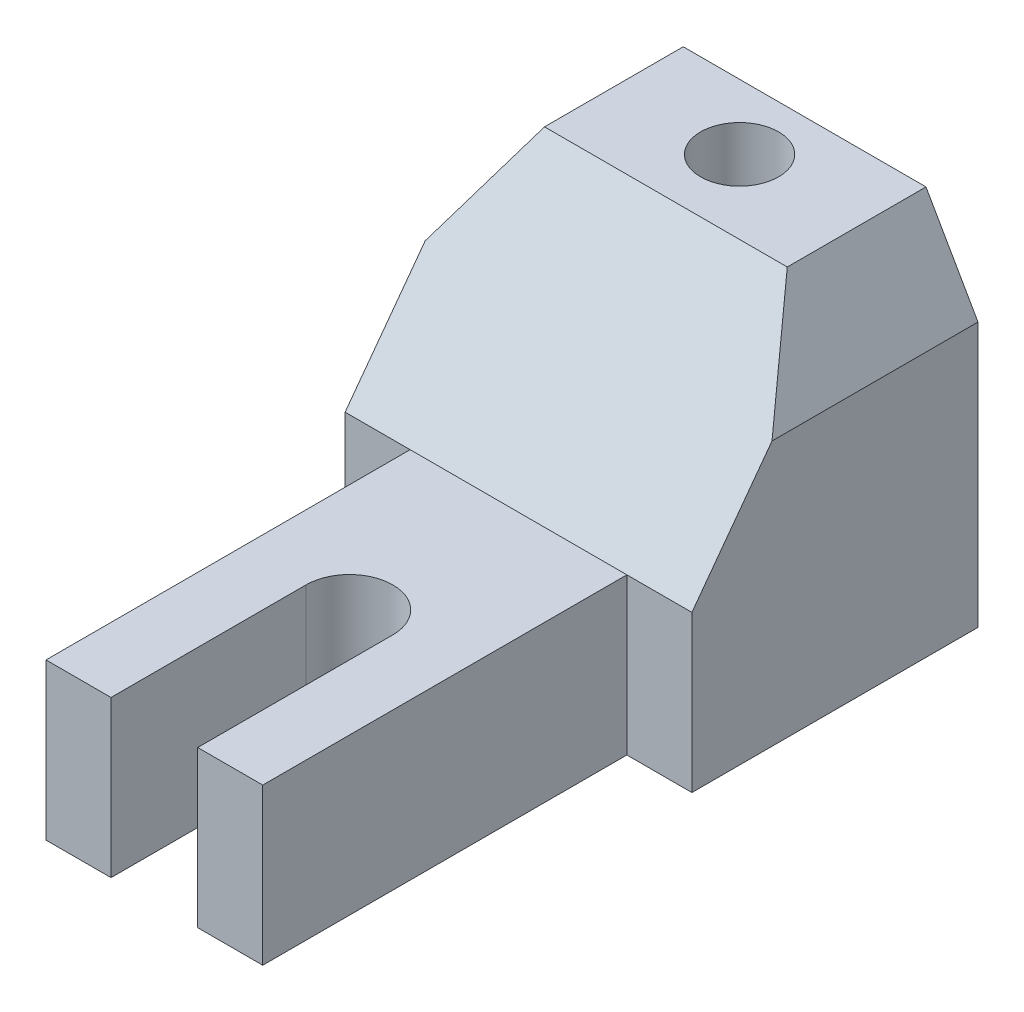
SolidWorks part; units mm, degrees
ref_plane "Alzado" through (0, 0, 0) normal (0, 0, 1) x (1, 0, 0)
ref_plane "Planta" through (0, 0, 0) normal (0, 1, 0) x (1, 0, 0)
ref_plane "Vista lateral" through (0, 0, 0) normal (1, 0, 0) x (0, 0, -1)
sketch "Croquis1" plane through (0, 0, 0) normal (0, 1, 0) x (1, 0, 0)
  line L1 (18.7624, -27.6609) -> (98.7624, -27.6609)
  line L2 (18.7624, -27.6609) -> (18.7624, 122.3391)
  line L3 (18.7624, 122.3391) -> (98.7624, 122.3391)
  line L4 (98.7624, -27.6609) -> (98.7624, 122.3391)
  dimension "D1" = 80
  dimension "D2" = 150
extrude "Saliente-Extruir1" add sketch "Croquis1" along normal blind 82
sketch "Croquis2" plane through (0, 0, -122.3391) normal (0, 0, -1) x (-1, 0, 0)
  line L0 (-98.7624, 82) -> (-98.7624, 61)
  line L1 (-98.7624, 82) -> (-98.7624, 0) construction
  line L2 (-98.7624, 61) -> (-86.7624, 82)
  line L3 (-98.7624, 82) -> (-18.7624, 82) construction
  line L4 (-86.7624, 82) -> (-98.7624, 82)
  line L5 (-18.7624, 82) -> (-30.7624, 82)
  line L6 (-30.7624, 82) -> (-18.7624, 61)
  line L7 (-18.7624, 82) -> (-18.7624, 0) construction
  line L8 (-18.7624, 61) -> (-18.7624, 82)
  dimension "D1" = 21
  dimension "D2" = 12
  dimension "D3" = 21
  dimension "D4" = 12
extrude "Cortar-Extruir1" cut sketch "Croquis2" against normal blind 150
sketch "Croquis3" plane through (0, 82, 0) normal (0, 1, 0) x (1, 0, 0)
  line L0 (98.7624, -27.6609) -> (98.7624, 122.3391) construction
  line L1 (86.7624, 122.3391) -> (30.7624, 122.3391) construction
  line L2 (30.7624, -27.6609) -> (86.7624, -27.6609) construction
  line L3 (48.7624, 17.3391) -> (48.7624, -27.6609)
  line L4 (68.7624, 17.3391) -> (68.7624, -27.6609)
  line L5 (18.7624, -27.6609) -> (18.7624, 122.3391) construction
  line L6 (18.7624, 56.3391) -> (33.7624, 56.3391)
  line L7 (18.7624, 56.3391) -> (18.7624, -27.6609)
  line L8 (18.7624, -27.6609) -> (33.7624, -27.6609)
  line L9 (33.7624, 56.3391) -> (33.7624, -27.6609)
  line L11 (98.7624, 56.3391) -> (83.7624, 56.3391)
  line L12 (98.7624, 56.3391) -> (98.7624, -27.6609)
  line L13 (98.7624, -27.6609) -> (83.7624, -27.6609)
  line L14 (83.7624, 56.3391) -> (83.7624, -27.6609)
  circle A0 centre (58.7624, 107.3391) radius 9
  arc A1 (68.7624, 17.3391) -> (48.7624, 17.3391) centre (58.7624, 17.3391) ccw
  line M1 (30.7624, -27.6609) -> (86.7624, -27.6609)
  line M2 (86.7624, -27.6609) -> (86.7624, 122.3391)
  line M4 (30.7624, 122.3391) -> (30.7624, -27.6609)
  dimension "D3" = 20
  dimension "D4" = 18
  dimension "D1" = 40
  dimension "D2" = 15
  dimension "D5" = 45
  dimension "D6" = 40
  dimension "D7" = 84
  dimension "D8" = 15
  dimension "D9" = 15
  dimension "D10" = 84
extrude "Cortar-Extruir2" cut sketch "Croquis3" against normal blind 150 contours A0 | L4 A1 L3 M1 | L7 L8 L6 M4 | L9 L6 M4 M1 | L13 L12 L11 M2 | L11 L14 M1 M2
sketch "Croquis4" plane through (98.7624, 0, 0) normal (1, 0, 0) x (0, 0, -1)
  line L0 (-27.6609, 36) -> (56.3391, 36)
  line L1 (-27.6609, 0) -> (-27.6609, 82) construction
  line L2 (56.3391, 0) -> (56.3391, 82) construction
  line L3 (56.3391, 36) -> (90.3391, 82)
  line L4 (56.3391, 82) -> (122.3391, 82) construction
  line L5 (90.3391, 82) -> (-27.6609, 82)
  line L6 (-27.6609, 82) -> (-27.6609, 36)
  dimension "D1" = 32
  dimension "D2" = 36
extrude "Cortar-Extruir3" cut sketch "Croquis4" against normal blind 80
